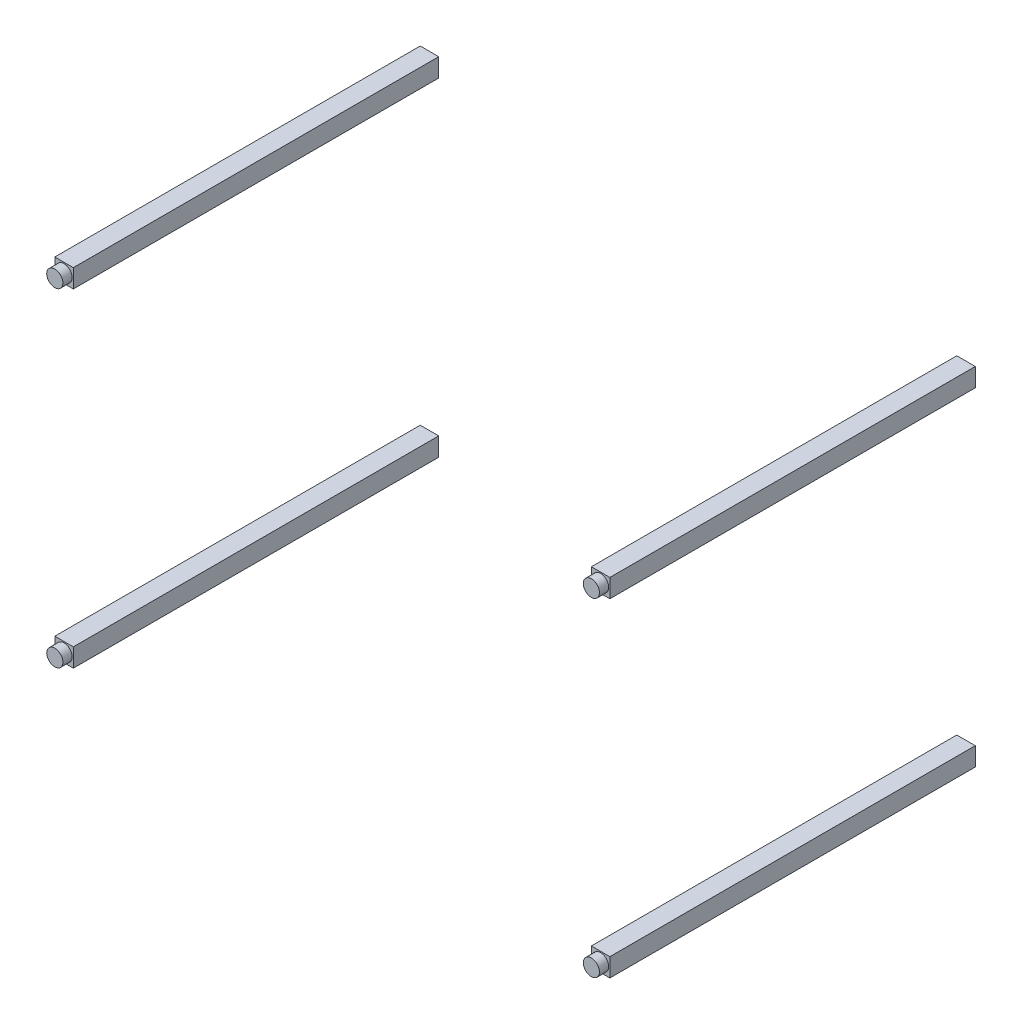
SolidWorks part; units mm, degrees
ref_plane "Front Plane" through (0, 0, 0) normal (0, 0, 1) x (1, 0, 0)
ref_plane "Top Plane" through (0, 0, 0) normal (0, 1, 0) x (1, 0, 0)
ref_plane "Right Plane" through (0, 0, 0) normal (1, 0, 0) x (0, 0, -1)
sketch "Sketch2" plane through (0, 0, 39) normal (0, 0, 1) x (1, 0, 0)
  line L6 (-600, 375) -> (-560, 375)
  line L7 (-600, 375) -> (-600, 335)
  line L8 (-600, 335) -> (-560, 335)
  line L9 (-560, 375) -> (-560, 335)
  line L10 (0, 0) -> (0, 696.2698) construction
  line L11 (0, 0) -> (-2134.8907, 0) construction
  line L12 (600, 335) -> (560, 335)
  line L13 (560, 375) -> (560, 335)
  line L14 (600, 375) -> (560, 375)
  line L15 (600, 375) -> (600, 335)
  line L16 (600, -375) -> (600, -335)
  line L17 (600, -375) -> (560, -375)
  line L18 (560, -375) -> (560, -335)
  line L19 (600, -335) -> (560, -335)
  line L20 (-600, -335) -> (-560, -335)
  line L21 (-560, -375) -> (-560, -335)
  line L22 (-600, -375) -> (-560, -375)
  line L23 (-600, -375) -> (-600, -335)
  dimension "D1" = 40
  dimension "D2" = 40
extrude "Boss-Extrude1" add sketch "Sketch2" along normal blind 790
sketch "Sketch3" plane through (0, 0, 829) normal (0, 0, 1) x (1, 0, 0)
  line L0 (-560, 355) -> (-600, 355) construction
  line L1 (-560, 335) -> (-560, 375) construction
  line L2 (-600, -375) -> (-600, 375) construction
  line L3 (0, 0) -> (0, 668.4836) construction
  line L4 (0, 0) -> (-1027.5617, 0) construction
  circle A0 centre (-580, 355) radius 17.5
  circle A1 centre (580, 355) radius 17.5
  circle A2 centre (-580, -355) radius 17.5
  circle A3 centre (580, -355) radius 17.5
  dimension "D1" = 35
extrude "Boss-Extrude2" add sketch "Sketch3" along normal blind 20
